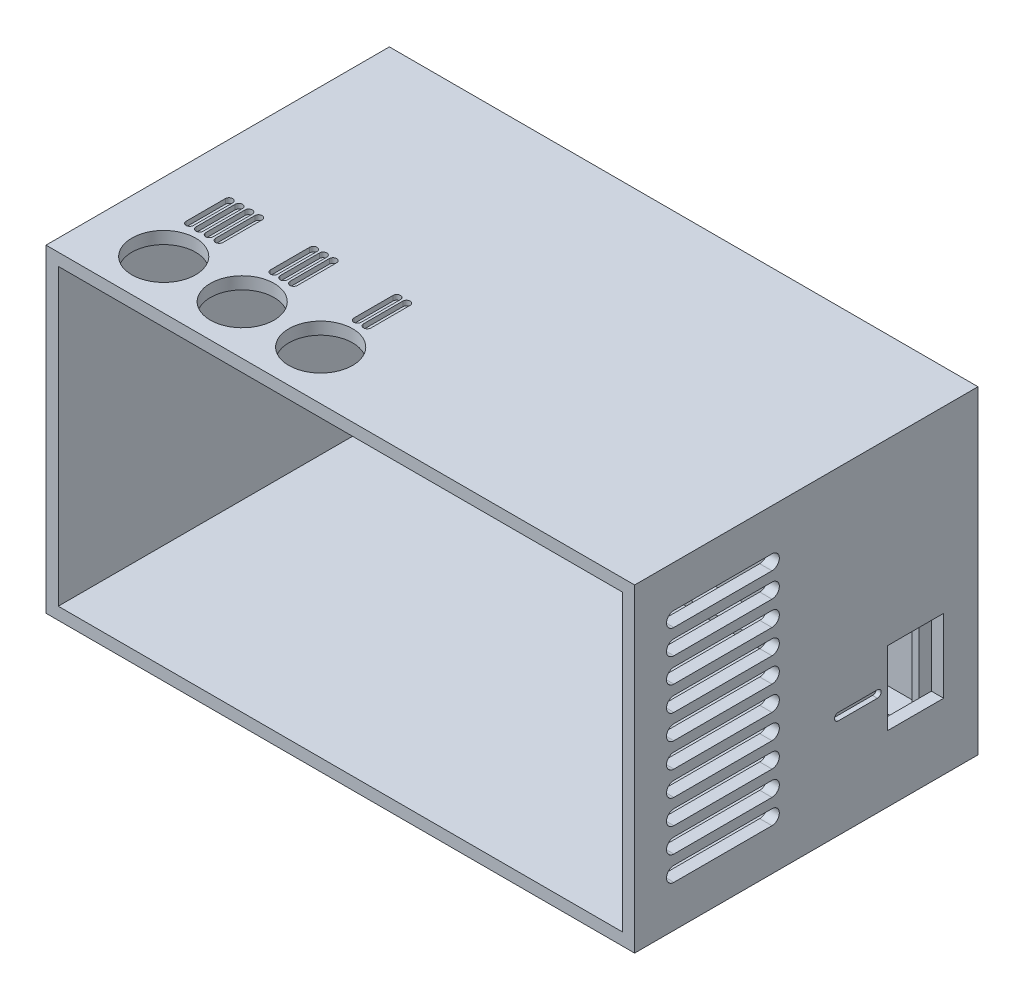
SolidWorks part; units mm, degrees
ref_plane "Front Plane" through (0, 0, 0) normal (0, 0, 1) x (1, 0, 0)
ref_plane "Top Plane" through (0, 0, 0) normal (0, 1, 0) x (1, 0, 0)
ref_plane "Right Plane" through (0, 0, 0) normal (1, 0, 0) x (0, 0, -1)
ref_plane "Plane1" through (0, 0, 2.5) normal (0, 0, -1) x (-1, 0, 0)
sketch "Sketch1" plane through (0, 0, 2.5) normal (0, 0, -1) x (-1, 0, 0)
  line L0 (-12.5, 57) -> (-12.5, 18)
  line L1 (-12.5, 18) -> (-10, 20.5)
  line L2 (-10, 20.5) -> (-10, 54.5)
  line L3 (-10, 54.5) -> (-12.5, 57)
extrude "Boss-Extrude1" add sketch "Sketch1" against normal blind 5
sketch "Sketch2" plane through (12.5, 0, 0) normal (1, 0, 0) x (0, 0, -1)
  line L0 (-2.5, 57) -> (-2.5, 18)
  line L1 (-2.5, 18) -> (-7.5, 18)
  line L2 (-7.5, 18) -> (-7.5, 57)
  line L3 (-7.5, 57) -> (-2.5, 57)
extrude "Boss-Extrude2" add sketch "Sketch2" along normal blind 103
sketch "Sketch3" plane through (0, 18, 0) normal (0, -1, 0) x (1, 0, 0)
  line L0 (117.5, 2.5) -> (0, 2.5)
  line L1 (0, 2.5) -> (0, 70)
  line L2 (0, 70) -> (117.5, 70)
  line L3 (117.5, 70) -> (117.5, 2.5)
extrude "Boss-Extrude3" add sketch "Sketch3" along normal blind 18
sketch "Sketch4" plane through (0, 18, 0) normal (0, 1, 0) x (-1, 0, 0)
  line L0 (0, 2.5) -> (-2.5, 2.5)
  line L1 (-2.5, 2.5) -> (-2.5, 70)
  line L2 (-2.5, 70) -> (0, 70)
  line L3 (0, 70) -> (0, 2.5)
extrude "Boss-Extrude4" add sketch "Sketch4" along normal blind 39
sketch "Sketch5" plane through (0, 57, 0) normal (0, 1, 0) x (-1, 0, 0)
  line L0 (0, 2.5) -> (-117.5, 2.5)
  line L1 (-117.5, 2.5) -> (-117.5, 70)
  line L2 (-117.5, 70) -> (0, 70)
  line L3 (0, 70) -> (0, 2.5)
extrude "Boss-Extrude5" add sketch "Sketch5" along normal blind 8
sketch "Sketch6" plane through (0, 57, 0) normal (0, -1, 0) x (1, 0, 0)
  line L0 (115.5, 7.5) -> (115.5, 2.5)
  line L1 (115.5, 2.5) -> (117.5, 2.5)
  line L2 (117.5, 2.5) -> (117.5, 70)
  line L3 (117.5, 70) -> (2.5, 70)
  line L4 (2.5, 70) -> (2.5, 2.5)
  line L5 (2.5, 2.5) -> (12.5, 2.5)
  line L6 (12.5, 2.5) -> (12.5, 7.5)
  line L7 (12.5, 7.5) -> (115.5, 7.5)
extrude "Cut-Extrude1" cut sketch "Sketch6" against normal blind 4
sketch "Sketch7" plane through (0, 0, 2.5) normal (0, 0, -1) x (-1, 0, 0)
  line L0 (-117.5, 0) -> (-117.5, 65)
  line L1 (-117.5, 65) -> (0, 65)
  line L2 (0, 65) -> (0, 0)
  line L3 (0, 0) -> (-117.5, 0)
extrude "Boss-Extrude6" add sketch "Sketch7" along normal blind 2.5
sketch "Sketch8" plane through (0, 61, 0) normal (0, -1, 0) x (1, 0, 0)
  line L0 (117.5, 70) -> (2.5, 70)
  line L1 (2.5, 70) -> (2.5, 2.5)
  line L2 (2.5, 2.5) -> (117.5, 2.5)
  line L3 (117.5, 2.5) -> (117.5, 70)
extrude "Cut-Extrude2" cut sketch "Sketch8" against normal blind 1.5
sketch "Sketch9" plane through (0, 18, 0) normal (0, 1, 0) x (-1, 0, 0)
  line L0 (-115.5, 2.5) -> (-115.5, 7.5)
  line L1 (-115.5, 7.5) -> (-12.5, 7.5)
  line L2 (-12.5, 7.5) -> (-12.5, 2.5)
  line L3 (-12.5, 2.5) -> (-2.5, 2.5)
  line L4 (-2.5, 2.5) -> (-2.5, 70)
  line L5 (-2.5, 70) -> (-117.5, 70)
  line L6 (-117.5, 70) -> (-117.5, 2.5)
  line L7 (-117.5, 2.5) -> (-115.5, 2.5)
extrude "Cut-Extrude3" cut sketch "Sketch9" against normal blind 14
sketch "Sketch10" plane through (0, 4, 0) normal (0, 1, 0) x (-1, 0, 0)
  line L0 (-117.5, 2.5) -> (-2.5, 2.5)
  line L1 (-2.5, 2.5) -> (-2.5, 70)
  line L2 (-2.5, 70) -> (-117.5, 70)
  line L3 (-117.5, 70) -> (-117.5, 2.5)
extrude "Cut-Extrude4" cut sketch "Sketch10" against normal blind 1.5
sketch "Sketch11" plane through (117.5, 0, 0) normal (1, 0, 0) x (0, 0, -1)
  line L0 (0, 0) -> (-70, 0)
  line L1 (-70, 0) -> (-70, 65)
  line L2 (-70, 65) -> (0, 65)
  line L3 (0, 65) -> (0, 0)
extrude "Boss-Extrude7" add sketch "Sketch11" along normal blind 2.5
sketch "Sketch12" plane through (0, 0, 7.5) normal (0, 0, 1) x (1, 0, 0)
  line L0 (114, 5.5) -> (114, 59.5)
  line L1 (114, 59.5) -> (14, 59.5)
  line L2 (14, 59.5) -> (14, 56.5)
  line L3 (14, 56.5) -> (11.5, 54)
  line L4 (11.5, 54) -> (11.5, 21)
  line L5 (11.5, 21) -> (14, 21)
  line L6 (14, 21) -> (14, 5.5)
  line L7 (14, 5.5) -> (114, 5.5)
extrude "Cut-Extrude5" cut sketch "Sketch12" against normal blind 1.5
sketch "Sketch13" plane through (0, 0, 6) normal (0, 0, 1) x (1, 0, 0)
  line L0 (14, 21) -> (14, 5.5)
  line L1 (14, 5.5) -> (114, 5.5)
  line L2 (114, 5.5) -> (114, 59.5)
  line L3 (114, 59.5) -> (18, 59.5)
  line L4 (18, 59.5) -> (18, 58.5)
  line L5 (14, 56.5) -> (11.5, 54)
  line L6 (11.5, 54) -> (11.5, 21)
  line L7 (11.5, 21) -> (14, 21)
  arc A0 (18, 58.5) -> (14, 56.5) centre (15.5, 58.5) cw
extrude "Cut-Extrude6" cut sketch "Sketch13" against normal blind 3.5
sketch "Sketch14" plane through (117.5, 0, 0) normal (-1, 0, 0) x (0, 0, 1)
  line L0 (42, 53.5) -> (62, 53.5)
  line L1 (62, 56.5) -> (42, 56.5)
  arc A0 (42, 56.5) -> (42, 53.5) centre (42, 55) ccw
  arc A1 (62, 53.5) -> (62, 56.5) centre (62, 55) ccw
extrude "Cut-Extrude7" cut sketch "Sketch14" against normal through all
sketch "Sketch15" plane through (117.5, 0, 0) normal (-1, 0, 0) x (0, 0, 1)
  line L0 (42, 48.5) -> (62, 48.5)
  line L1 (62, 51.5) -> (42, 51.5)
  arc A0 (42, 51.5) -> (42, 48.5) centre (42, 50) ccw
  arc A1 (62, 48.5) -> (62, 51.5) centre (62, 50) ccw
extrude "Cut-Extrude8" cut sketch "Sketch15" against normal through all
sketch "Sketch16" plane through (117.5, 0, 0) normal (-1, 0, 0) x (0, 0, 1)
  line L0 (42, 43.5) -> (62, 43.5)
  line L1 (62, 46.5) -> (42, 46.5)
  arc A0 (42, 46.5) -> (42, 43.5) centre (42, 45) ccw
  arc A1 (62, 43.5) -> (62, 46.5) centre (62, 45) ccw
extrude "Cut-Extrude9" cut sketch "Sketch16" against normal through all
sketch "Sketch17" plane through (117.5, 0, 0) normal (-1, 0, 0) x (0, 0, 1)
  line L0 (42, 38.5) -> (62, 38.5)
  line L1 (62, 41.5) -> (42, 41.5)
  arc A0 (42, 41.5) -> (42, 38.5) centre (42, 40) ccw
  arc A1 (62, 38.5) -> (62, 41.5) centre (62, 40) ccw
extrude "Cut-Extrude10" cut sketch "Sketch17" against normal through all
sketch "Sketch18" plane through (117.5, 0, 0) normal (-1, 0, 0) x (0, 0, 1)
  line L0 (42, 33.5) -> (62, 33.5)
  line L1 (62, 36.5) -> (42, 36.5)
  arc A0 (42, 36.5) -> (42, 33.5) centre (42, 35) ccw
  arc A1 (62, 33.5) -> (62, 36.5) centre (62, 35) ccw
extrude "Cut-Extrude11" cut sketch "Sketch18" against normal through all
sketch "Sketch19" plane through (117.5, 0, 0) normal (-1, 0, 0) x (0, 0, 1)
  line L0 (42, 28.5) -> (62, 28.5)
  line L1 (62, 31.5) -> (42, 31.5)
  arc A0 (42, 31.5) -> (42, 28.5) centre (42, 30) ccw
  arc A1 (62, 28.5) -> (62, 31.5) centre (62, 30) ccw
extrude "Cut-Extrude12" cut sketch "Sketch19" against normal through all
sketch "Sketch20" plane through (117.5, 0, 0) normal (-1, 0, 0) x (0, 0, 1)
  line L0 (42, 23.5) -> (62, 23.5)
  line L1 (62, 26.5) -> (42, 26.5)
  arc A0 (42, 26.5) -> (42, 23.5) centre (42, 25) ccw
  arc A1 (62, 23.5) -> (62, 26.5) centre (62, 25) ccw
extrude "Cut-Extrude13" cut sketch "Sketch20" against normal through all
sketch "Sketch21" plane through (117.5, 0, 0) normal (-1, 0, 0) x (0, 0, 1)
  line L0 (42, 18.5) -> (62, 18.5)
  line L1 (62, 21.5) -> (42, 21.5)
  arc A0 (42, 21.5) -> (42, 18.5) centre (42, 20) ccw
  arc A1 (62, 18.5) -> (62, 21.5) centre (62, 20) ccw
extrude "Cut-Extrude14" cut sketch "Sketch21" against normal through all
sketch "Sketch22" plane through (117.5, 0, 0) normal (-1, 0, 0) x (0, 0, 1)
  line L0 (62, 11.5) -> (42, 11.5)
  line L1 (42, 8.5) -> (62, 8.5)
  arc A0 (62, 8.5) -> (62, 11.5) centre (62, 10) ccw
  arc A1 (42, 11.5) -> (42, 8.5) centre (42, 10) ccw
extrude "Cut-Extrude15" cut sketch "Sketch22" against normal through all
sketch "Sketch23" plane through (117.5, 0, 0) normal (-1, 0, 0) x (0, 0, 1)
  line L0 (42, 13.5) -> (62, 13.5)
  line L1 (62, 16.5) -> (42, 16.5)
  arc A0 (42, 16.5) -> (42, 13.5) centre (42, 15) ccw
  arc A1 (62, 13.5) -> (62, 16.5) centre (62, 15) ccw
extrude "Cut-Extrude16" cut sketch "Sketch23" against normal through all
sketch "Sketch24" plane through (120, 0, 0) normal (1, 0, 0) x (0, 0, -1)
  line L0 (-18.5, 28.5) -> (-18.5, 13.5)
  line L1 (-18.5, 13.5) -> (-7, 13.5)
  line L2 (-7, 13.5) -> (-7, 28.5)
  line L3 (-7, 28.5) -> (-18.5, 28.5)
  line L4 (0, 0) -> (0, 65) construction
  line L5 (-70, 0) -> (0, 0) construction
  dimension "D1" = 7
  dimension "D2" = 11.5
  dimension "D3" = 13.5
  dimension "D4" = 15
extrude "Cut-Extrude17" cut sketch "Sketch24" against normal up to next
sketch "Sketch25" plane through (0, 0, 2.5) normal (0, 0, 1) x (1, 0, 0)
  line L0 (102, 8) -> (102, 5.5)
  line L1 (102, 5.5) -> (97, 5.5)
  line L2 (97, 5.5) -> (97, 8)
  arc A0 (97, 8) -> (102, 8) centre (99.5, 8) cw
extrude "Boss-Extrude8" add sketch "Sketch25" along normal blind 3.5
sketch "Sketch26" plane through (0, 0, 2.5) normal (0, 0, 1) x (1, 0, 0)
  line L0 (25, 8) -> (25, 5.5)
  line L1 (25, 5.5) -> (20, 5.5)
  line L2 (20, 5.5) -> (20, 8)
  arc A0 (20, 8) -> (25, 8) centre (22.5, 8) cw
extrude "Boss-Extrude9" add sketch "Sketch26" along normal blind 3.5
sketch "Sketch27" plane through (0, 0, 2.5) normal (0, 0, 1) x (1, 0, 0)
  line L0 (97, 57) -> (97, 59.5)
  line L1 (97, 59.5) -> (102, 59.5)
  line L2 (102, 59.5) -> (102, 57)
  arc A0 (102, 57) -> (97, 57) centre (99.5, 57) cw
extrude "Boss-Extrude10" add sketch "Sketch27" along normal blind 3.5
draft "Draft1" type of draft neutral plane draft angle 45 faces to draft 1 face at (12.75, 21, 5) neutral plane through (11.5, 54, 6) neutral plane normal (1, 0, 0) parameters "D1"=45
hole_wizard "Ø3.0 (3) Diameter Hole1" positions "Sketch29" profile "Sketch28" hole size "Ø3.0" standard "ANSI Metric"
sketch "Sketch29" plane through (0, 0, 0) normal (0, 0, -1) x (-1, 0, 0)
  point P0 (-22.5, 8)
sketch "Sketch28" plane through (22.5, 8, 0) normal (1, 0, 0) x (0, 1, 0)
  line L0 (0, 0) -> (0, 70)
  line L1 (0, 70) -> (1.5, 70)
  line L2 (1.5, 70) -> (1.5, 0)
  line L5 (1.5, 0) -> (0, 0)
  line L11 (0, -6.35) -> (0, 107.95) construction
  dimension "Thru Hole Dia." = 3
  dimension "Thru Hole Depth" = 70
hole_wizard "Ø3.0 (3) Diameter Hole2" positions "Sketch31" profile "Sketch30" hole size "Ø3.0" standard "ANSI Metric"
sketch "Sketch31" plane through (0, 0, 0) normal (0, 0, -1) x (-1, 0, 0)
  point P2 (-99.5, 57)
  point P3 (0, 0)
  point P4 (0, 0)
sketch "Sketch30" plane through (99.5, 57, 0) normal (1, 0, 0) x (0, 1, 0)
  line L0 (0, 0) -> (0, 6)
  line L1 (0, 6) -> (1.5, 6)
  line L2 (1.5, 6) -> (1.5, 0)
  line L5 (1.5, 0) -> (0, 0)
  line L10 (0, 6) -> (-1.5, 6) construction
  line L11 (0, -6.35) -> (0, 107.95) construction
  dimension "Hole Dia." = 3
  dimension "Hole Depth" = 6
  dimension "Drill Angle" = 180
hole_wizard "Ø13.0 (13) Diameter Hole1" positions "Sketch33" profile "Sketch32" hole size "Ø13.0" standard "ANSI Metric"
sketch "Sketch33" plane through (0, 65, 0) normal (0, 1, 0) x (1, 0, 0)
  point P0 (14, -60)
  point P1 (46, -60)
  point P2 (30, -60)
sketch "Sketch32" plane through (14, 65, 60) normal (1, 0, 0) x (0, 0, 1)
  line L0 (0, 0) -> (0, 2.5)
  line L1 (0, 2.5) -> (6.5, 2.5)
  line L2 (6.5, 2.5) -> (6.5, 0)
  line L5 (6.5, 0) -> (0, 0)
  line L11 (0, -6.35) -> (0, 107.95) construction
  dimension "Thru Hole Dia." = 13
  dimension "Thru Hole Depth" = 2.5
ref_plane "Plane2" through (0, 0, 51.25) normal (0, 0, 1) x (1, 0, 0)
sketch "Sketch36" plane through (120, 0, 0) normal (1, 0, 0) x (0, 0, -1)
  line L0 (-28.5, 21) -> (-20.5, 21) construction
  line L1 (-28.5, 21.75) -> (-20.5, 21.75)
  line L2 (-28.5, 20.25) -> (-20.5, 20.25)
  arc A0 (-28.5, 21.75) -> (-28.5, 20.25) centre (-28.5, 21) ccw
  arc A1 (-20.5, 20.25) -> (-20.5, 21.75) centre (-20.5, 21) ccw
  point P0 (-18.5, 13.5)
  point P1 (-18.5, 28.5)
  point P3 (-7, 13.5)
  point P5 (-7, 28.5)
  point P10 (-24.5, 21)
  dimension "D1" = 7.5
  dimension "D2" = 8
  dimension "D3" = 1.5
  dimension "D4" = 2
extrude "Cut-Extrude18" cut sketch "Sketch36" against normal blind 1
sketch "Sketch37" plane through (0, 65, 0) normal (0, 1, 0) x (1, 0, 0)
  line L0 (45, -43.5) -> (45, -51.5) construction
  line L1 (45.75, -43.5) -> (45.75, -51.5)
  line L2 (44.25, -43.5) -> (44.25, -51.5)
  line L3 (47, -43.5) -> (47, -51.5) construction
  line L4 (47.75, -43.5) -> (47.75, -51.5)
  line L5 (46.25, -43.5) -> (46.25, -51.5)
  line L6 (28, -43.5) -> (28, -51.5) construction
  line L7 (28.75, -43.5) -> (28.75, -51.5)
  line L8 (27.25, -43.5) -> (27.25, -51.5)
  line L9 (30, -43.5) -> (30, -51.5) construction
  line L10 (30.75, -43.5) -> (30.75, -51.5)
  line L11 (29.25, -43.5) -> (29.25, -51.5)
  line L12 (32, -43.5) -> (32, -51.5) construction
  line L13 (32.75, -43.5) -> (32.75, -51.5)
  line L14 (31.25, -43.5) -> (31.25, -51.5)
  line L15 (10.8167, -43.5026) -> (10.8167, -51.5026) construction
  line L16 (11.5667, -43.5026) -> (11.5667, -51.5026)
  line L17 (10.0667, -43.5026) -> (10.0667, -51.5026)
  line L18 (12.8167, -43.5026) -> (12.8167, -51.5026) construction
  line L19 (13.5667, -43.5026) -> (13.5667, -51.5026)
  line L20 (12.0667, -43.5026) -> (12.0667, -51.5026)
  line L21 (14.8167, -43.5026) -> (14.8167, -51.5026) construction
  line L22 (15.5667, -43.5026) -> (15.5667, -51.5026)
  line L23 (14.0667, -43.5026) -> (14.0667, -51.5026)
  line L24 (16.8167, -43.5026) -> (16.8167, -51.5026) construction
  line L25 (17.5667, -43.5026) -> (17.5667, -51.5026)
  line L26 (16.0667, -43.5026) -> (16.0667, -51.5026)
  arc A0 (45.75, -43.5) -> (44.25, -43.5) centre (45, -43.5) ccw
  arc A1 (44.25, -51.5) -> (45.75, -51.5) centre (45, -51.5) ccw
  arc A2 (47.75, -43.5) -> (46.25, -43.5) centre (47, -43.5) ccw
  circle A3 centre (46, -60) radius 6.5 construction
  arc A4 (46.25, -51.5) -> (47.75, -51.5) centre (47, -51.5) ccw
  arc A5 (28.75, -43.5) -> (27.25, -43.5) centre (28, -43.5) ccw
  arc A6 (27.25, -51.5) -> (28.75, -51.5) centre (28, -51.5) ccw
  arc A7 (30.75, -43.5) -> (29.25, -43.5) centre (30, -43.5) ccw
  arc A8 (29.25, -51.5) -> (30.75, -51.5) centre (30, -51.5) ccw
  arc A9 (32.75, -43.5) -> (31.25, -43.5) centre (32, -43.5) ccw
  arc A10 (31.25, -51.5) -> (32.75, -51.5) centre (32, -51.5) ccw
  arc A11 (11.5667, -43.5026) -> (10.0667, -43.5026) centre (10.8167, -43.5026) ccw
  arc A12 (10.0667, -51.5026) -> (11.5667, -51.5026) centre (10.8167, -51.5026) ccw
  arc A13 (13.5667, -43.5026) -> (12.0667, -43.5026) centre (12.8167, -43.5026) ccw
  arc A14 (12.0667, -51.5026) -> (13.5667, -51.5026) centre (12.8167, -51.5026) ccw
  arc A15 (15.5667, -43.5026) -> (14.0667, -43.5026) centre (14.8167, -43.5026) ccw
  arc A16 (14.0667, -51.5026) -> (15.5667, -51.5026) centre (14.8167, -51.5026) ccw
  arc A17 (17.5667, -43.5026) -> (16.0667, -43.5026) centre (16.8167, -43.5026) ccw
  arc A18 (16.0667, -51.5026) -> (17.5667, -51.5026) centre (16.8167, -51.5026) ccw
  circle A19 centre (30, -60) radius 6.5 construction
  circle A20 centre (14, -60) radius 6.5 construction
  point P2 (45, -47.5)
  point P7 (46, -53.5)
  point P12 (47, -47.5)
  point P17 (28, -47.5)
  point P24 (30, -47.5)
  point P31 (32, -47.5)
  point P38 (10.8167, -47.5026)
  point P45 (12.8167, -47.5026)
  point P52 (14.8167, -47.5026)
  point P59 (16.8167, -47.5026)
  point P66 (30, -53.5)
  point P67 (13.8167, -53.5026)
  dimension "D1" = 8
  dimension "D2" = 1.5
  dimension "D3" = 2
  dimension "D4" = 8
  dimension "D5" = 1.5
  dimension "D6" = 8
  dimension "D7" = 8
  dimension "D8" = 8
  dimension "D9" = 1.5
  dimension "D10" = 1.5
  dimension "D11" = 1.5
  dimension "D12" = 8
  dimension "D13" = 1.5
  dimension "D14" = 8
  dimension "D15" = 1.5
  dimension "D16" = 8
  dimension "D17" = 1.5
  dimension "D18" = 8
  dimension "D19" = 1.5
  dimension "D20" = 1
  dimension "D21" = 1
  dimension "D22" = 2
  dimension "D23" = 2
  dimension "D24" = 2
  dimension "D25" = 2
  dimension "D26" = 2
  dimension "D27" = 2
  dimension "D28" = 2
  dimension "D29" = 1
  dimension "D30" = 2
  dimension "D31" = 2
  dimension "D32" = 0
  dimension "D33" = 2
  dimension "D34" = 0
  dimension "D35" = 2
  dimension "D36" = 0
extrude "Cut-Extrude19" cut sketch "Sketch37" against normal blind 1
